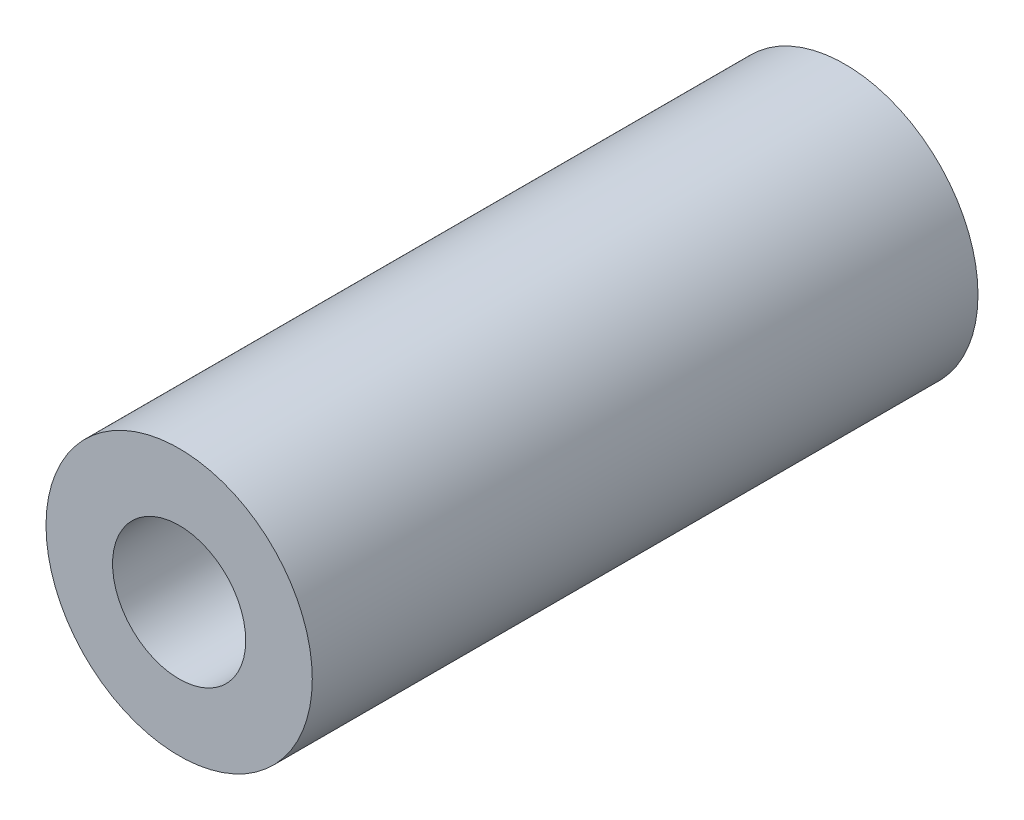
SolidWorks part; units mm, degrees
ref_plane "Front Plane" through (0, 0, 0) normal (0, 0, 1) x (1, 0, 0)
ref_plane "Top Plane" through (0, 0, 0) normal (0, 1, 0) x (1, 0, 0)
ref_plane "Right Plane" through (0, 0, 0) normal (1, 0, 0) x (0, 0, -1)
sketch "Sketch1" plane through (0, 0, 0) normal (0, 0, 1) x (1, 0, 0)
  circle A0 centre (0, 0) radius 2
  circle A1 centre (0, 0) radius 4
  dimension "D1" = 4
  dimension "D2" = 8
extrude "Boss-Extrude1" add sketch "Sketch1" along normal blind 20
